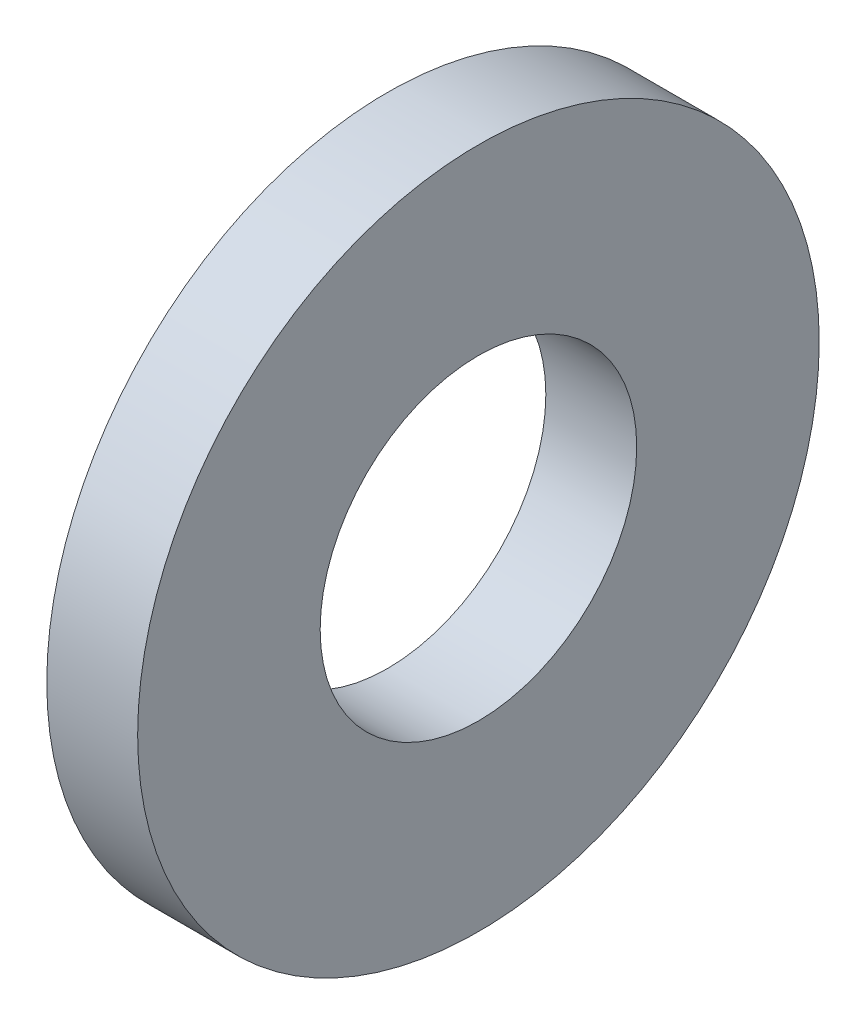
SolidWorks part; units mm, degrees
ref_plane "Plane1" through (0, 0, 0) normal (0, 0, 1) x (1, 0, 0)
ref_plane "Plane2" through (0, 0, 0) normal (0, 1, 0) x (1, 0, 0)
ref_plane "Plane3" through (0, 0, 0) normal (1, 0, 0) x (0, 0, -1)
sketch "Sketch1" plane through (0, 0, 0) normal (0, 0, 1) x (1, 0, 0)
  line L0 (-34.925, 0) -> (9.525, 0) construction
  line L1 (0, 2.09) -> (0, 4.5)
  line L2 (0, 4.5) -> (-1.2, 4.5)
  line L3 (-1.2, 4.5) -> (-1.2, 2.09)
  line L4 (-1.2, 2.09) -> (0, 2.09)
  dimension "Thickness" = 1.2
  dimension "Inside_dia" = 4.18
  dimension "Outside_dia" = 9
revolve "Base-Revolve" add sketch "Sketch1" angle 360 about L0
